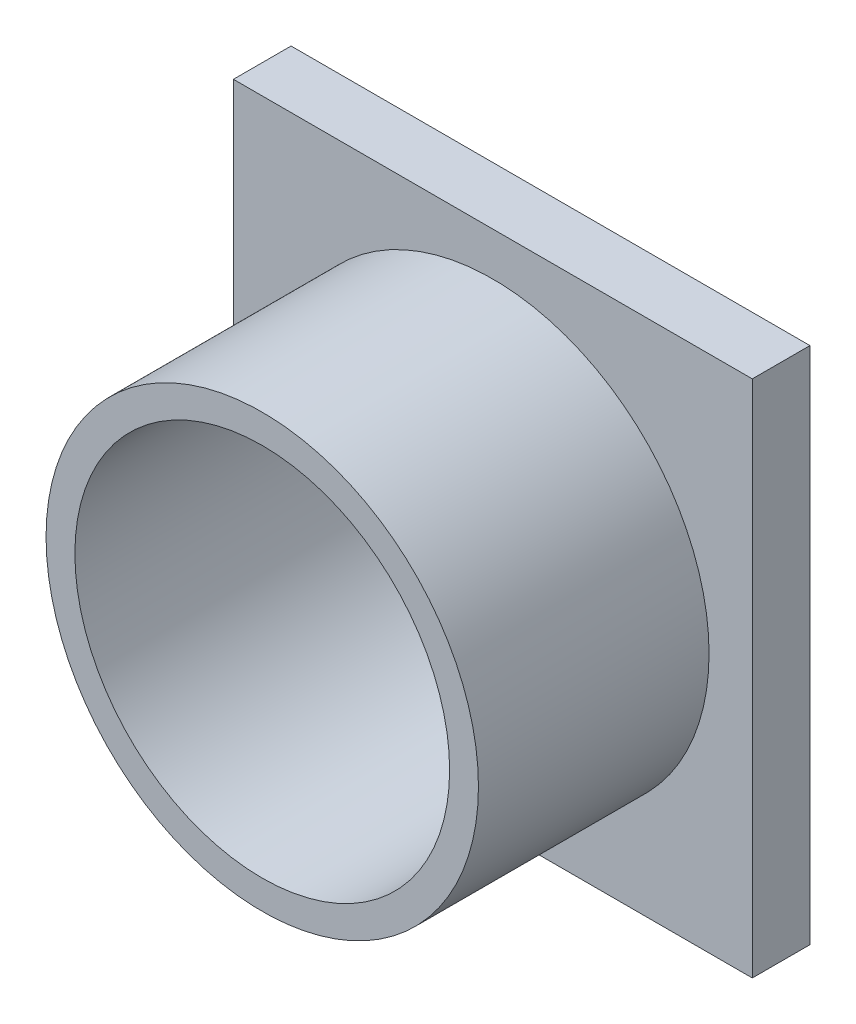
SolidWorks part; units mm, degrees
ref_plane "Plan de face" through (0, 0, 0) normal (0, 0, 1) x (1, 0, 0)
ref_plane "Plan de dessus" through (0, 0, 0) normal (0, 1, 0) x (1, 0, 0)
ref_plane "Plan de droite" through (0, 0, 0) normal (1, 0, 0) x (0, 0, -1)
sketch "Esquisse1" plane through (0, 0, 0) normal (0, 0, 1) x (1, 0, 0)
  line L1 (-22.5, 22.5) -> (22.5, 22.5)
  line L2 (-22.5, 22.5) -> (-22.5, -22.5)
  line L3 (-22.5, -22.5) -> (22.5, -22.5)
  line L4 (22.5, 22.5) -> (22.5, -22.5)
  line L5 (-22.5, 22.5) -> (22.5, -22.5) construction
  line L6 (-22.5, -22.5) -> (22.5, 22.5) construction
  circle A0 centre (0, 0) radius 16.25
  point P0 (0, 0)
  dimension "D1" = 32.5
  dimension "D2" = 45
  dimension "D3" = 45
extrude "Boss.-Extru.1" add sketch "Esquisse1" along normal blind 5
sketch "Esquisse2" plane through (0, 0, 5) normal (0, 0, 1) x (1, 0, 0)
  circle A0 centre (0, 0) radius 16.25
  circle A1 centre (0, 0) radius 18.75
  dimension "D1" = 32.5
  dimension "D2" = 37.5
extrude "Boss.-Extru.2" add sketch "Esquisse2" along normal blind 20
sketch "Esquisse3" plane through (0, 0, 0) normal (0, 0, -1) x (-1, 0, 0)
  line L0 (0, 22.5) -> (0, -22.5) construction
  line L1 (-22.5, 22.5) -> (22.5, 22.5) construction
  line L2 (22.5, -22.5) -> (-22.5, -22.5) construction
  line L3 (-22.5, 0) -> (22.5, 0) construction
  line L4 (-22.5, -22.5) -> (-22.5, 22.5) construction
  line L5 (22.5, 22.5) -> (22.5, -22.5) construction
  line L6 (14, 18.8) -> (14, 15)
  line L7 (-18.8, 18.8) -> (-14, 18.8)
  line L8 (-18.8, 18.8) -> (-18.8, 15)
  line L9 (-18.8, 15) -> (-14, 15)
  line L10 (-14, 18.8) -> (-14, 15)
  line L11 (-18.8, 18.8) -> (-14, 15) construction
  line L12 (-18.8, 15) -> (-14, 18.8) construction
  line L13 (18.8, 15) -> (14, 15)
  line L14 (18.8, 18.8) -> (18.8, 15)
  line L15 (18.8, 18.8) -> (14, 18.8)
  line L16 (-14, -18.8) -> (-14, -15)
  line L17 (-18.8, -15) -> (-14, -15)
  line L18 (-18.8, -18.8) -> (-18.8, -15)
  line L19 (-18.8, -18.8) -> (-14, -18.8)
  line L20 (18.8, -18.8) -> (14, -18.8)
  line L21 (18.8, -18.8) -> (18.8, -15)
  line L22 (18.8, -15) -> (14, -15)
  line L23 (14, -18.8) -> (14, -15)
  point P12 (-16.4, 16.9)
  dimension "D1" = 4.8
  dimension "D2" = 3.8
  dimension "D3" = 3.7
  dimension "D4" = 3.7
extrude "Boss.-Extru.3" add sketch "Esquisse3" along normal blind 3
